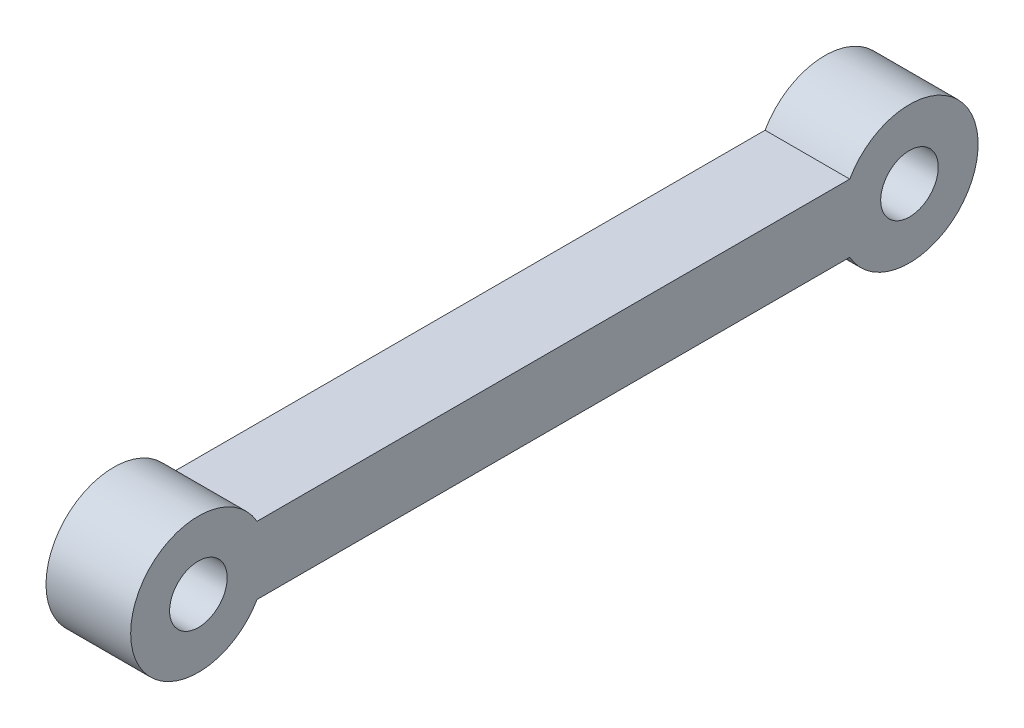
SolidWorks part; units mm, degrees
ref_plane "Спереди" through (0, 0, 0) normal (0, 0, 1) x (1, 0, 0)
ref_plane "Сверху" through (0, 0, 0) normal (0, 1, 0) x (1, 0, 0)
ref_plane "Справа" through (0, 0, 0) normal (1, 0, 0) x (0, 0, -1)
other "Configuration Table"
sketch "Эскиз1" plane through (0.7582, 0, 0) normal (-1, 0, 0) x (0, 0, 1)
  line L0 (-2.0677, 57.8148) -> (-14.2214, 57.8148) construction
  line L1 (-40.5318, 59.8148) -> (-5.5318, 59.8148)
  line L3 (-40.5318, 55.8148) -> (-5.5318, 55.8148)
  arc A0 (-5.5318, 55.8148) -> (-5.5318, 59.8148) centre (-2.0677, 57.8148) ccw
  circle A1 centre (-2.0677, 57.8148) radius 1.7
  arc A2 (-40.5318, 59.8148) -> (-40.5318, 55.8148) centre (-44.0593, 57.8148) ccw
  circle A3 centre (-44.0593, 57.8148) radius 1.7
  dimension "D1" = 8
  dimension "D2" = 3.4
  dimension "D4" = 8.11
  dimension "D5" = 3.4
  dimension "D3" = 4
  dimension "D6" = 35
extrude "Бобышка-Вытянуть1" add sketch "Эскиз1" along normal blind 5
